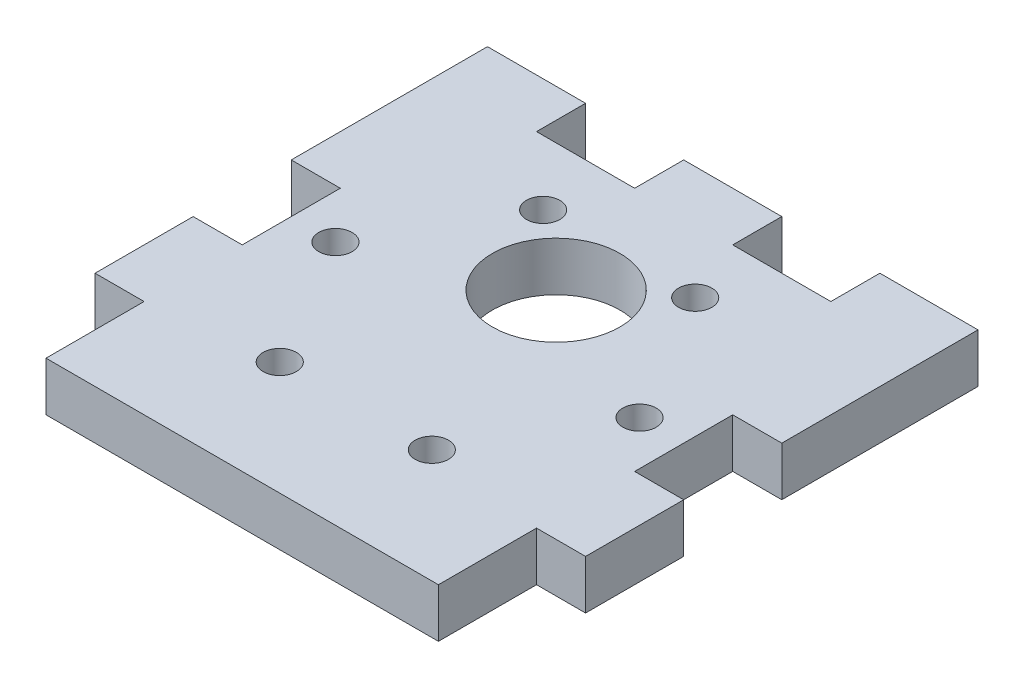
SolidWorks part; units mm, degrees
ref_plane "前视基准面" through (0, 0, 0) normal (0, 0, 1) x (1, 0, 0)
ref_plane "上视基准面" through (0, 0, 0) normal (0, 1, 0) x (1, 0, 0)
ref_plane "右视基准面" through (0, 0, 0) normal (1, 0, 0) x (0, 0, -1)
sketch "草图1" plane through (0, 0, 0) normal (0, 1, 0) x (1, 0, 0)
  line L0 (0, -49.9299) -> (0, 49.9299) construction
  line L1 (-25, -25) -> (25, -25)
  line L2 (-25, -25) -> (-25, 25)
  line L3 (-25, 25) -> (25, 25)
  line L4 (25, -25) -> (25, 25)
  line L5 (-25, -25) -> (25, 25) construction
  line L6 (-25, 25) -> (25, -25) construction
  circle A1 centre (0, 0) radius 15.5 construction
  circle A2 centre (-15.5, 0) radius 1.7
  circle A3 centre (-7.75, 13.4234) radius 1.7
  circle A4 centre (7.75, 13.4234) radius 1.7
  circle A5 centre (15.5, 0) radius 1.7
  circle A6 centre (7.75, -13.4234) radius 1.7
  circle A7 centre (-7.75, -13.4234) radius 1.7
  circle A8 centre (0, 7) radius 6.5
  point P1 (0, 0)
  point P18 (0, 0)
  point P26 (0, 0)
  dimension "D1" = 50
  dimension "D2" = 31
  dimension "D3" = 3.4
  dimension "D6" = 13
  dimension "D5" = 7
  dimension "D7" = 50
  dimension "D4" = 6
extrude "凸台-拉伸1" add sketch "草图1" along normal blind 5
sketch "草图6" plane through (0, 5, 0) normal (0, 1, 0) x (1, 0, 0)
  line L6 (25, 25) -> (-25, 25) construction
  line L7 (-15, 25) -> (-5, 25)
  line L8 (-15, 25) -> (-15, 20)
  line L9 (-15, 20) -> (-5, 20)
  line L10 (-5, 25) -> (-5, 20)
  line L11 (-25, 25) -> (-25, -25) construction
  line L12 (5, 25) -> (15, 25)
  line L13 (5, 25) -> (5, 20)
  line L14 (5, 20) -> (15, 20)
  line L15 (15, 25) -> (15, 20)
  line L16 (-25, -25) -> (-20, -25)
  line L17 (-25, -25) -> (-25, -15)
  line L18 (-25, -15) -> (-20, -15)
  line L19 (-20, -25) -> (-20, -15)
  line L20 (-25, -5) -> (-20, -5)
  line L21 (-25, -5) -> (-25, 5)
  line L22 (-25, 5) -> (-20, 5)
  line L23 (-20, -5) -> (-20, 5)
  line L24 (25, -25) -> (25, 25) construction
  line L25 (25, -25) -> (20, -25)
  line L26 (25, -25) -> (25, -15)
  line L27 (25, -15) -> (20, -15)
  line L28 (20, -25) -> (20, -15)
  line L29 (25, -5) -> (20, -5)
  line L30 (25, -5) -> (25, 5)
  line L31 (25, 5) -> (20, 5)
  line L32 (20, -5) -> (20, 5)
  dimension "D1" = 5
  dimension "D2" = 10
  dimension "D3" = 10
  dimension "D4" = 10
  dimension "D5" = 10
extrude "切除-拉伸1" cut sketch "草图6" against normal through all
